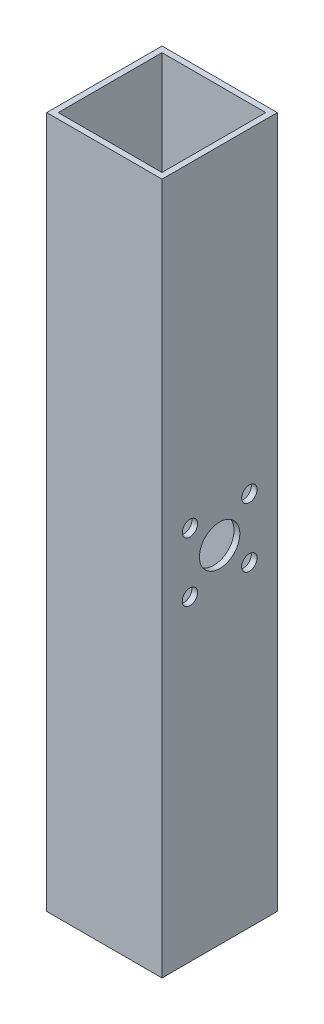
SolidWorks part; units mm, degrees
ref_plane "Front Plane" through (0, 0, 0) normal (0, 0, 1) x (1, 0, 0)
ref_plane "Top Plane" through (0, 0, 0) normal (0, 1, 0) x (1, 0, 0)
ref_plane "Right Plane" through (0, 0, 0) normal (1, 0, 0) x (0, 0, -1)
sketch "Sketch1" plane through (0, 0, 0) normal (0, 1, 0) x (1, 0, 0)
  line L0 (0, 76.2) -> (76.2, 0) construction
  line L1 (0, 0) -> (76.2, 0)
  line L2 (0, 0) -> (0, 76.2)
  line L3 (0, 76.2) -> (76.2, 76.2)
  line L4 (76.2, 0) -> (76.2, 76.2)
  line L5 (76.2, 76.2) -> (0, 0) construction
  line L6 (3.81, 72.39) -> (72.39, 72.39)
  line L7 (72.39, 3.81) -> (72.39, 72.39)
  line L8 (3.81, 3.81) -> (72.39, 3.81)
  line L9 (3.81, 3.81) -> (3.81, 72.39)
  dimension "D3" = 3.81
  dimension "D1" = 76.2
  dimension "D2" = 76.2
extrude "Boss-Extrude1" add sketch "Sketch1" along normal blind 457.2
sketch "Sketch2" plane through (0, 0, 0) normal (-1, 0, 0) x (0, 0, 1)
  line L1 (-38.1, 457.2) -> (-38.1, 0) construction
  line L2 (-76.2, 457.2) -> (0, 457.2) construction
  line L3 (-76.2, 0) -> (0, 0) construction
  circle A0 centre (-38.1, 228.6) radius 13.335
  dimension "D1" = 26.67
extrude "Cut-Extrude1" cut sketch "Sketch2" against normal blind 914.4
sketch "Sketch3" plane through (0, 0, 0) normal (-1, 0, 0) x (0, 0, 1)
  circle A6 centre (-57.7424, 248.2424) radius 5.08
  circle A7 centre (-18.4576, 248.2424) radius 5.08
  circle A8 centre (-57.7424, 208.9576) radius 5.08
  circle A9 centre (-18.4576, 208.9576) radius 5.08
  point P17 (-38.1, 228.6)
extrude "Cut-Extrude2" cut sketch "Sketch3" against normal blind 914.4
